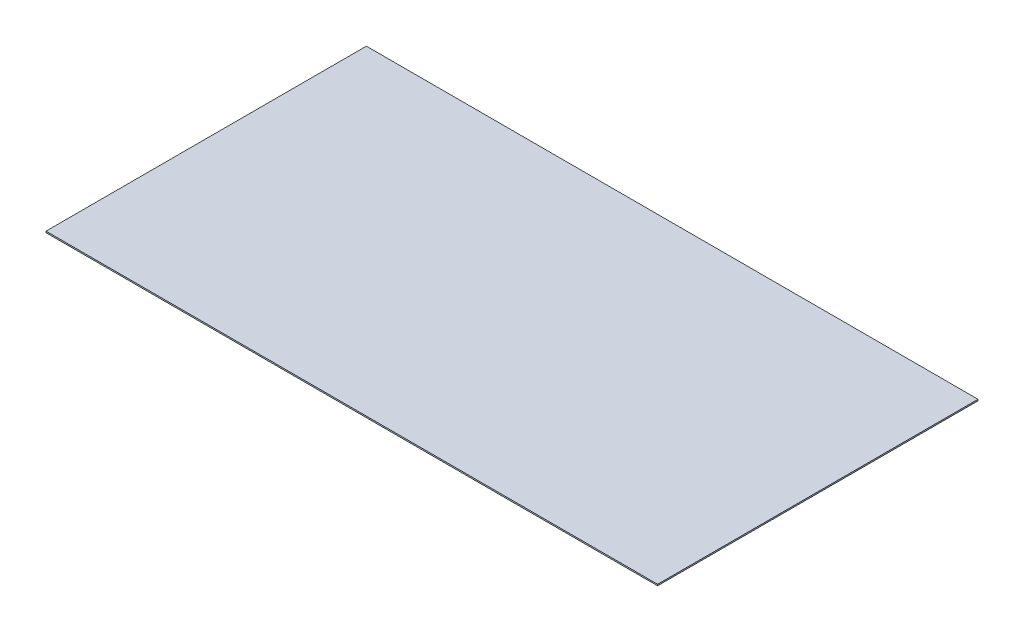
SolidWorks part; units mm, degrees
material "5052-O"
ref_plane "Front Plane" through (0, 0, 0) normal (0, 0, 1) x (1, 0, 0)
ref_plane "Top Plane" through (0, 0, 0) normal (0, 1, 0) x (1, 0, 0)
ref_plane "Right Plane" through (0, 0, 0) normal (1, 0, 0) x (0, 0, -1)
sketch "Sketch1" plane through (0, 0, 0) normal (0, 1, 0) x (1, 0, 0)
  line L1 (-1050, 550) -> (1050, 550)
  line L2 (-1050, 550) -> (-1050, -550)
  line L3 (-1050, -550) -> (1050, -550)
  line L4 (1050, 550) -> (1050, -550)
  line L5 (-1050, 550) -> (1050, -550) construction
  line L6 (-1050, -550) -> (1050, 550) construction
  point P0 (0, 0)
  dimension "D1" = 1100
  dimension "D2" = 2100
extrude "Boss-Extrude1" add sketch "Sketch1" along normal blind 4.7625
sketch "Sketch2" plane through (0, 0, 0) normal (0, 1, 0) x (1, 0, 0)
  line L0 (-1003.9688, -520.7) -> (-1003.9688, -609.6) construction
  line L1 (-1003.9688, -520.7) -> (1003.9688, -520.7)
  line L2 (-1003.9688, -520.7) -> (-1003.9688, 520.7)
  line L3 (-1003.9688, 520.7) -> (1003.9688, 520.7)
  line L4 (1003.9688, -520.7) -> (1003.9688, 520.7)
  line L5 (1092.8688, -638.9) -> (1092.8688, 638.9) construction
  line L7 (-1092.8688, -609.6) -> (1092.8688, -609.6)
  line L8 (-1092.8688, -609.6) -> (-1092.8688, 609.6)
  line L9 (-1092.8688, 609.6) -> (1092.8688, 609.6)
  line L10 (1092.8688, -609.6) -> (1092.8688, 609.6)
  line L12 (-1003.9688, 609.6) -> (1003.9688, 609.6) construction
  line L17 (-1003.9688, -520.7) -> (1003.9688, -520.7) construction
  line L18 (-1003.9688, -609.6) -> (1003.9688, -609.6) construction
  line L19 (-1092.8688, -638.9) -> (-1092.8688, 638.9) construction
  line L20 (1003.9688, -638.9) -> (1003.9688, 638.9) construction
  line L21 (-1003.9688, 520.7) -> (1003.9688, 520.7) construction
  point P0 (0, 0)
  point P6 (-20.8295, 11.6187)
split line "Split Line1" [suppressed]
equation "\"D1@Sketch1\"=\"absorber_plate_width\""
equation "\"D2@Sketch1\"=\"absorber_plate_length\""
equation "\"absorber_plate_width\" = 1100mm"
equation "\"absorber_plate_length\" = 2100mm"
equation "\"absorber_plate_thickness\" = .1875in"
equation "\"groove_depth\" = 20mm"
equation "\"frame_thickness\" = 60mm"
equation "\"bend_radius\"= 10mm"
equation "\"insulation_thickness\" = 50mm"
equation "\"D1@Boss-Extrude1\"=\"absorber_plate_thickness\""
